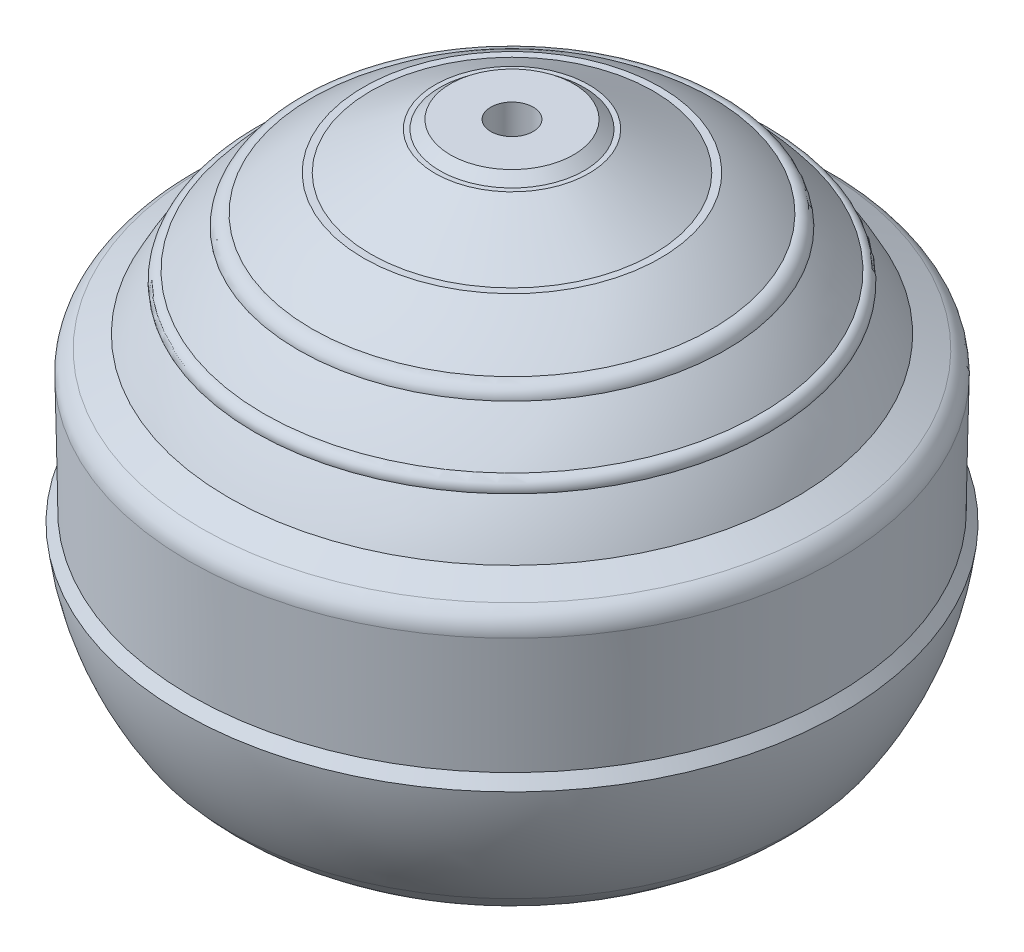
SolidWorks part; units mm, degrees
material "3.3549 (EN-AW 5182)"
ref_plane "Front Plane" through (0, 0, 0) normal (0, 0, 1) x (1, 0, 0)
ref_plane "Top Plane" through (0, 0, 0) normal (0, 1, 0) x (1, 0, 0)
ref_plane "Right Plane" through (0, 0, 0) normal (1, 0, 0) x (0, 0, -1)
sketch "Sketch1" plane through (0, 0, 0) normal (0, 0, 1) x (1, 0, 0)
  line L0 (0, 0) -> (0, -2.0338)
  line L1 (9.2555, -21.6377) -> (10.2575, -21.6377)
  line L2 (14, -14.8465) -> (13.65, -14.3817)
  line L3 (13.65, -14.3817) -> (13.7388, -9.38)
  line L4 (13.182, -8.4658) -> (12.0358, -7.8994)
  line L5 (6.302, -1.9598) -> (6.002, -1.9598)
  line L6 (6.002, -1.9598) -> (3.2662, -0.3598)
  line L7 (3.2662, -0.3598) -> (3.0662, -0.3598)
  line L8 (3.0662, -0.3598) -> (2.6164, 0)
  line L9 (0, 0) -> (0.9, 0)
  line L10 (2.6164, 0) -> (0.9, 0)
  line L11 (0, -2.0338) -> (0.9, -2.0338)
  arc A0 (10.2575, -21.6377) -> (12.0358, -20.1628) centre (7.3054, -16.2689) ccw
  arc A1 (13.7388, -9.38) -> (13.182, -8.4658) centre (12.7389, -9.3623) ccw
  arc A2 (12.0358, -7.8994) -> (10.9196, -6.0598) centre (-0.4558, -14.2208) ccw
  arc A3 (10.9196, -6.0598) -> (10.5436, -5.5598) centre (10.5268, -5.9638) ccw
  arc A4 (10.5436, -5.5598) -> (9.0685, -3.9598) centre (-0.4558, -14.2208) ccw
  arc A5 (9.0685, -3.9598) -> (8.4997, -3.4598) centre (8.5313, -3.9974) ccw
  arc A6 (8.4997, -3.4598) -> (6.302, -1.9598) centre (-0.4558, -14.2208) ccw
  arc A7 (9.2555, -21.6377) -> (0.9, -2.0338) centre (0, -14) ccw
  arc A8 (12.0358, -20.1628) -> (14, -14.8465) centre (2.08, -13.4634) ccw
revolve "Revolve1" add sketch "Sketch1" angle 360 about L0
sketch "Sketch2" plane through (0, 0, 0) normal (0, 1, 0) x (1, 0, 0)
  circle A0 centre (0, 0) radius 0.9
extrude "Cut-Extrude1" cut sketch "Sketch2" against normal blind 10
